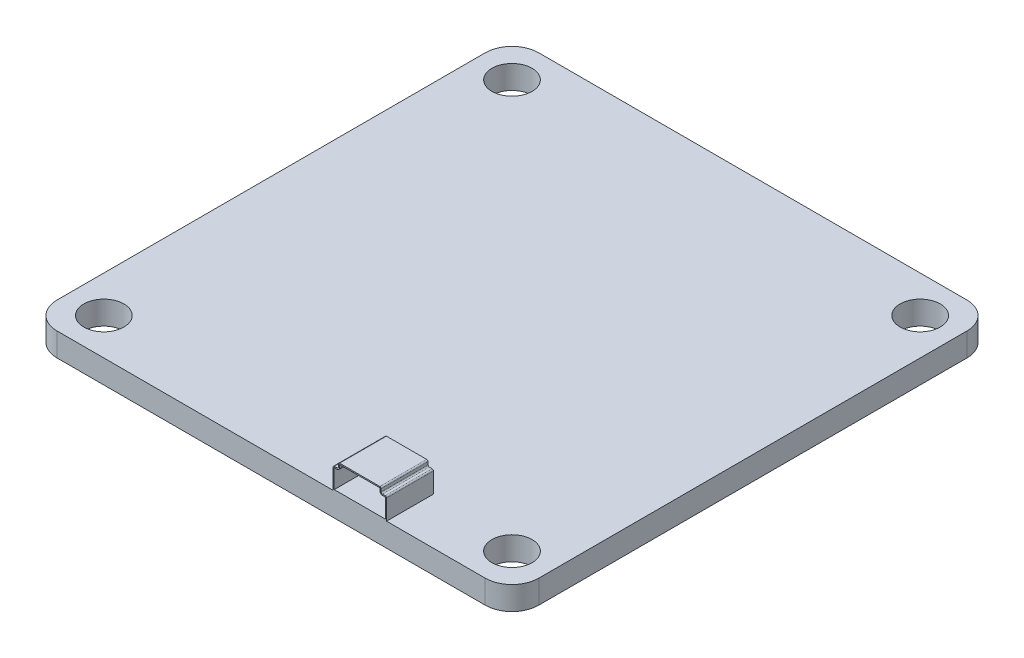
SolidWorks part; units mm, degrees
ref_plane "Front Plane" through (0, 0, 0) normal (0, 0, 1) x (1, 0, 0)
ref_plane "Top Plane" through (0, 0, 0) normal (0, 1, 0) x (1, 0, 0)
ref_plane "Right Plane" through (0, 0, 0) normal (1, 0, 0) x (0, 0, -1)
sketch "Sketch1" plane through (0, 0, 0) normal (0, 1, 0) x (1, 0, 0)
  line L1 (16, -18) -> (-16, -18)
  line L2 (18, -16) -> (18, 16)
  line L3 (16, 18) -> (-16, 18)
  line L4 (-18, -16) -> (-18, 16)
  line L5 (18, -18) -> (-18, 18) construction
  line L6 (18, 18) -> (-18, -18) construction
  line L7 (-15.25, -15.25) -> (15.25, -15.25) construction
  line L8 (-15.25, -15.25) -> (-15.25, 15.25) construction
  line L9 (-15.25, 15.25) -> (15.25, 15.25) construction
  line L10 (15.25, -15.25) -> (15.25, 15.25) construction
  line L11 (-15.25, -15.25) -> (15.25, 15.25) construction
  line L12 (-15.25, 15.25) -> (15.25, -15.25) construction
  circle A0 centre (15.25, 15.25) radius 1.5
  circle A1 centre (-15.25, 15.25) radius 1.5
  circle A2 centre (15.25, -15.25) radius 1.5
  circle A3 centre (-15.25, -15.25) radius 1.5
  arc A4 (-16, 18) -> (-18, 16) centre (-16, 16) ccw
  arc A5 (-16, -18) -> (-18, -16) centre (-16, -16) cw
  arc A6 (16, -18) -> (18, -16) centre (16, -16) ccw
  arc A7 (18, 16) -> (16, 18) centre (16, 16) ccw
  point P0 (0, 0)
  point P6 (0, 0)
  dimension "D4" = 3
  dimension "D5" = 2
  dimension "D1" = 36
  dimension "D2" = 36
  dimension "D3" = 30.5
extrude "Boss-Extrude1" add sketch "Sketch1" along normal blind 1.75
sketch "Sketch2" plane through (0, 0, 18) normal (0, 0, 1) x (1, 0, 0)
  line L0 (-16, 1.75) -> (16, 1.75) construction
  line L1 (4.6258, 1.75) -> (8.6258, 1.75)
  line L2 (4.6258, 1.75) -> (4.6258, 3.25)
  line L3 (5.1258, 3.75) -> (8.1258, 3.75)
  line L4 (8.6258, 1.75) -> (8.6258, 3.25)
  line L5 (5.1258, 3.66) -> (8.1258, 3.66)
  line L6 (8.1358, 3.65) -> (8.1358, 3.45)
  line L7 (8.2258, 3.65) -> (8.2258, 3.45)
  line L8 (4.7258, 3.35) -> (4.9258, 3.35)
  line L9 (5.0258, 3.65) -> (5.0258, 3.45)
  line L10 (8.3258, 3.35) -> (8.5258, 3.35)
  line L11 (8.3258, 3.26) -> (8.5258, 3.26)
  line L12 (8.5358, 1.84) -> (8.5358, 3.25)
  line L13 (4.7158, 1.84) -> (8.5358, 1.84)
  line L14 (4.7158, 1.84) -> (4.7158, 3.25)
  line L15 (4.7258, 3.26) -> (4.9258, 3.26)
  line L16 (5.1158, 3.65) -> (5.1158, 3.45)
  arc A0 (8.5258, 3.35) -> (8.6258, 3.25) centre (8.5258, 3.25) cw
  arc A1 (8.2258, 3.45) -> (8.3258, 3.35) centre (8.3258, 3.45) ccw
  arc A2 (8.1258, 3.75) -> (8.2258, 3.65) centre (8.1258, 3.65) cw
  arc A3 (5.0258, 3.65) -> (5.1258, 3.75) centre (5.1258, 3.65) cw
  arc A4 (4.7258, 3.35) -> (4.6258, 3.25) centre (4.7258, 3.25) ccw
  arc A5 (4.9258, 3.35) -> (5.0258, 3.45) centre (4.9258, 3.45) ccw
  arc A6 (8.1258, 3.66) -> (8.1358, 3.65) centre (8.1258, 3.65) cw
  arc A7 (8.1358, 3.45) -> (8.3258, 3.26) centre (8.3258, 3.45) ccw
  arc A8 (8.5258, 3.26) -> (8.5358, 3.25) centre (8.5258, 3.25) cw
  arc A9 (4.7258, 3.26) -> (4.7158, 3.25) centre (4.7258, 3.25) ccw
  arc A10 (4.9258, 3.26) -> (5.1158, 3.45) centre (4.9258, 3.45) ccw
  arc A11 (5.1158, 3.65) -> (5.1258, 3.66) centre (5.1258, 3.65) cw
  point P14 (8.6258, 3.35)
  point P17 (8.2258, 3.35)
  point P20 (8.2258, 3.75)
  point P25 (4.6258, 3.35)
  point P28 (5.0258, 3.35)
  dimension "D7" = 0.1
  dimension "D1" = 0
  dimension "D2" = 4
  dimension "D3" = 2
  dimension "D4" = 0.4
  dimension "D5" = 0.4
  dimension "D6" = 0.4
  dimension "D8" = 0.09
extrude "Boss-Extrude2" add sketch "Sketch2" against normal blind 3
sketch "Sketch3" plane through (0, 0, 15) normal (0, 0, -1) x (-1, 0, 0)
  line L8 (-4.6258, 1.75) -> (-4.6258, 3.25)
  line L9 (-4.7258, 3.35) -> (-4.9258, 3.35)
  line L10 (-5.0258, 3.45) -> (-5.0258, 3.65)
  line L11 (-5.1258, 3.75) -> (-8.1258, 3.75)
  line L12 (-8.2258, 3.65) -> (-8.2258, 3.45)
  line L13 (-8.3258, 3.35) -> (-8.5258, 3.35)
  line L14 (-8.6258, 3.25) -> (-8.6258, 1.75)
  line L15 (-8.6258, 1.75) -> (-4.6258, 1.75)
  line L16 (-4.6258, 1.75) -> (-4.6258, 3.25)
  line L17 (-4.7258, 3.35) -> (-4.9258, 3.35)
  line L18 (-5.0258, 3.45) -> (-5.0258, 3.65)
  line L19 (-5.1258, 3.75) -> (-8.1258, 3.75)
  line L20 (-8.2258, 3.65) -> (-8.2258, 3.45)
  line L21 (-8.3258, 3.35) -> (-8.5258, 3.35)
  line L22 (-8.6258, 3.25) -> (-8.6258, 1.75)
  line L23 (-8.6258, 1.75) -> (-4.6258, 1.75)
  arc A6 (-4.6258, 3.25) -> (-4.7258, 3.35) centre (-4.7258, 3.25) ccw
  arc A7 (-5.0258, 3.45) -> (-4.9258, 3.35) centre (-4.9258, 3.45) ccw
  arc A8 (-5.0258, 3.65) -> (-5.1258, 3.75) centre (-5.1258, 3.65) ccw
  arc A9 (-8.1258, 3.75) -> (-8.2258, 3.65) centre (-8.1258, 3.65) ccw
  arc A10 (-8.3258, 3.35) -> (-8.2258, 3.45) centre (-8.3258, 3.45) ccw
  arc A11 (-8.5258, 3.35) -> (-8.6258, 3.25) centre (-8.5258, 3.25) ccw
  arc A12 (-4.6258, 3.25) -> (-4.7258, 3.35) centre (-4.7258, 3.25) ccw
  arc A13 (-5.0258, 3.45) -> (-4.9258, 3.35) centre (-4.9258, 3.45) ccw
  arc A14 (-5.0258, 3.65) -> (-5.1258, 3.75) centre (-5.1258, 3.65) ccw
  arc A15 (-8.1258, 3.75) -> (-8.2258, 3.65) centre (-8.1258, 3.65) ccw
  arc A16 (-8.3258, 3.35) -> (-8.2258, 3.45) centre (-8.3258, 3.45) ccw
  arc A17 (-8.5258, 3.35) -> (-8.6258, 3.25) centre (-8.5258, 3.25) ccw
  dimension "D1" = 0
extrude "Boss-Extrude3" add sketch "Sketch3" along normal blind 0.5
sketch "Sketch4" plane through (0, 0, 14.5) normal (0, 0, -1) x (-1, 0, 0)
  circle A0 centre (-5.6761, 2.5315) radius 0.3117
  circle A1 centre (-7.6412, 2.5315) radius 0.3117
  circle A2 centre (-6.6499, 2.5315) radius 0.3117
extrude "Cut-Extrude1" cut sketch "Sketch4" against normal up to next
